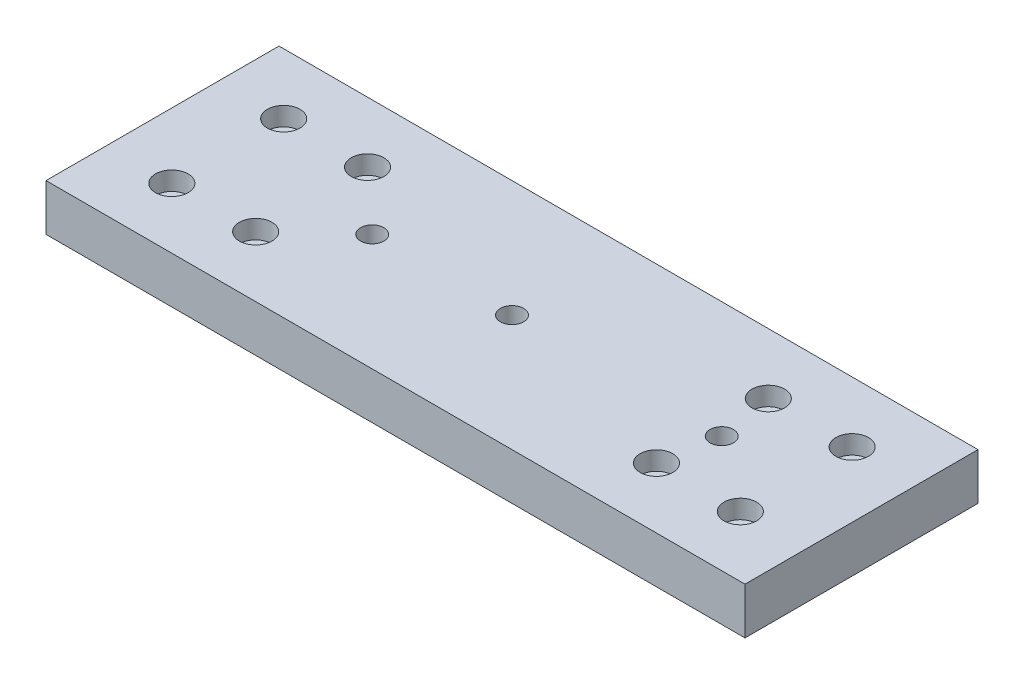
SolidWorks part; units mm, degrees
ref_plane "Front Plane" through (0, 0, 0) normal (0, 0, 1) x (1, 0, 0)
ref_plane "Top Plane" through (0, 0, 0) normal (0, 1, 0) x (1, 0, 0)
ref_plane "Right Plane" through (0, 0, 0) normal (1, 0, 0) x (0, 0, -1)
sketch "Sketch1" plane through (0, 0, 0) normal (0, 1, 0) x (1, 0, 0)
  line L1 (75, -25) -> (-75, -25)
  line L2 (75, -25) -> (75, 25)
  line L3 (75, 25) -> (-75, 25)
  line L4 (-75, -25) -> (-75, 25)
  line L5 (75, -25) -> (-75, 25) construction
  line L6 (75, 25) -> (-75, -25) construction
  point P0 (0, 0)
  dimension "D1" = 50
  dimension "D2" = 150
extrude "Boss-Extrude1" add sketch "Sketch1" along normal blind 10
sketch "Sketch2" plane through (0, 10, 0) normal (0, 1, 0) x (1, 0, 0)
  line L0 (-75, 0) -> (0, 0) construction
  line L1 (-75, 25) -> (-75, -25) construction
  line L2 (0, 0) -> (0, 25) construction
  line L3 (75, 25) -> (-75, 25) construction
  circle A0 centre (-43, -12) radius 1.5
  circle A1 centre (-61, -12) radius 1.5
  circle A3 centre (43, -12) radius 1.5
  circle A5 centre (61, -12) radius 1.5
  circle A7 centre (61, 12) radius 1.5
  circle A9 centre (43, 12) radius 1.5
  circle A12 centre (-61, 12) radius 1.5
  circle A16 centre (-43, 12) radius 1.5
  dimension "D1" = 3
  dimension "D2" = 24
  dimension "D3" = 18
  dimension "D4" = 14
extrude "Linear_bearing_mount" cut sketch "Sketch2" against normal through all
sketch "Sketch3" plane through (0, 0, 0) normal (0, -1, 0) x (1, 0, 0)
  line L2 (75, 25) -> (75, -25) construction
  circle A0 centre (0, 0) radius 2.5
  circle A1 centre (45, 0) radius 2.5
  circle A2 centre (-30, 0) radius 2.5
  dimension "D1" = 5
  dimension "D2" = 45
  dimension "D3" = 30
  dimension "D5" = 30
extrude "Surface_profile_mount" cut sketch "Sketch3" against normal through all
sketch "Sketch4" plane through (0, 0, 0) normal (0, -1, 0) x (1, 0, 0)
  circle A0 centre (45, 0) radius 4.25
  circle A1 centre (0, 0) radius 4.25
  circle A2 centre (-30, 0) radius 4.25
  dimension "D1" = 8.5
extrude "Surf.prof.mount_countersink" cut sketch "Sketch4" against normal blind 5
sketch "Sketch5" plane through (0, 10, 0) normal (0, 1, 0) x (1, 0, 0)
  line L0 (0, 25) -> (0, 0) construction
  line L1 (75, 25) -> (-75, 25) construction
  line L2 (0, 0) -> (-75, 0) construction
  line L3 (-75, 25) -> (-75, -25) construction
  circle A0 centre (-61, 12) radius 3.5
  circle A1 centre (-43, 12) radius 3.5
  circle A2 centre (-43, -12) radius 3.5
  circle A3 centre (-61, -12) radius 3.5
  circle A4 centre (61, -12) radius 3.5
  circle A5 centre (43, -12) radius 3.5
  circle A6 centre (43, 12) radius 3.5
  circle A7 centre (61, 12) radius 3.5
  dimension "D1" = 7
extrude "Cut-Extrude1" cut sketch "Sketch5" against normal blind 4
